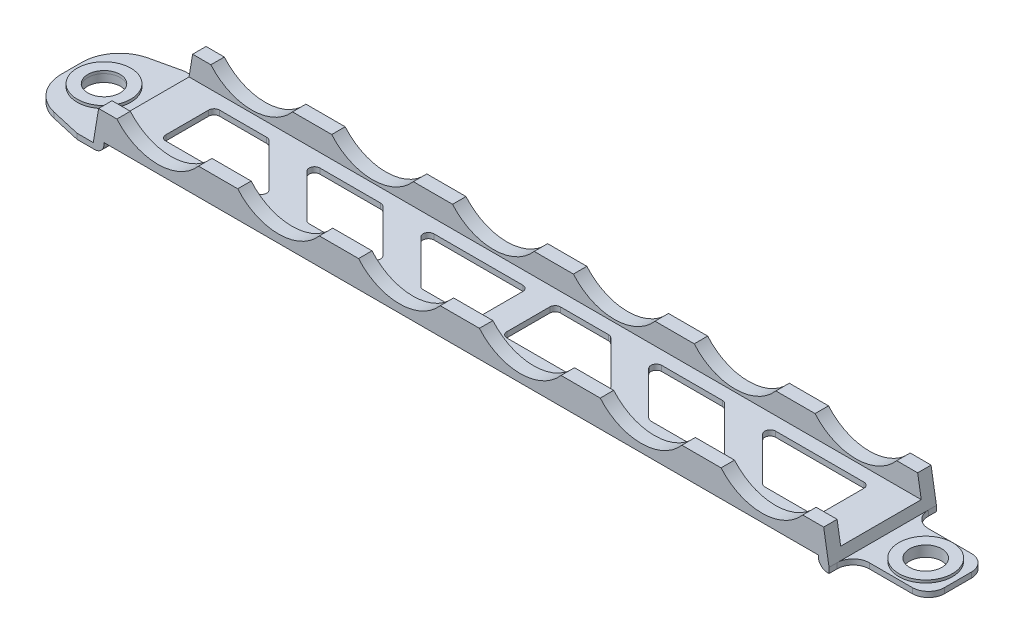
SolidWorks part; units mm, degrees
ref_plane "Front" through (0, 0, 0) normal (0, 0, 1) x (1, 0, 0)
ref_plane "Top" through (0, 0, 0) normal (0, 1, 0) x (1, 0, 0)
ref_plane "Right" through (0, 0, 0) normal (1, 0, 0) x (0, 0, -1)
sketch "Sketch1" plane through (0, 0, 0) normal (0, 1, 0) x (1, 0, 0)
  line L1 (-75.8645, 3.3155) -> (89.1355, 3.3155)
  line L2 (-75.8645, 3.3155) -> (-75.8645, -16.6845)
  line L3 (-75.8645, -16.6845) -> (89.1355, -16.6845)
  line L4 (89.1355, 3.3155) -> (89.1355, -16.6845)
  dimension "D1" = 165
  dimension "D2" = 20
extrude "Extrude1" add sketch "Sketch1" along normal blind 7
sketch "Sketch2" plane through (0, 7, 0) normal (0, 1, 0) x (-1, 0, 0)
  line L0 (-89.1355, 16.6845) -> (-89.1355, -3.3155) construction
  line L1 (75.8645, -0.8155) -> (-89.1355, -0.8155)
  line L2 (75.8645, -0.8155) -> (75.8645, 14.1845)
  line L3 (75.8645, 14.1845) -> (-89.1355, 14.1845)
  line L4 (-89.1355, -0.8155) -> (-89.1355, 14.1845)
  line L5 (75.8645, -3.3155) -> (75.8645, 16.6845) construction
  line L6 (-89.1355, -3.3155) -> (75.8645, -3.3155) construction
  line L7 (75.8645, 16.6845) -> (-89.1355, 16.6845) construction
  dimension "D1" = 2.5
  dimension "D2" = 2.5
extrude "Cut-Extrude2" cut sketch "Sketch2" against normal blind 4
sketch "Sketch3" plane through (0, 0, 16.6845) normal (0, 0, 1) x (1, 0, 0)
  line L0 (-75.8645, 0) -> (89.1355, 0) construction
  line L1 (-83.9413, 1) -> (-61.8645, 1)
  line L2 (-83.9413, 1) -> (-83.9413, 15.5971)
  line L3 (-83.9413, 15.5971) -> (-61.8645, 15.5971)
  line L4 (-61.8645, 1) -> (-61.8645, 15.5971)
  line L5 (-75.8645, 7) -> (-75.8645, 0) construction
  line L6 (6.6355, 7) -> (6.6355, 44.5919) construction
  line L7 (-75.8645, 7) -> (89.1355, 7) construction
  line L8 (75.1355, 1) -> (75.1355, 15.5971)
  line L9 (97.2124, 15.5971) -> (75.1355, 15.5971)
  line L10 (97.2124, 1) -> (97.2124, 15.5971)
  line L11 (97.2124, 1) -> (75.1355, 1)
  line L13 (-59.8645, -11.0368) -> (73.1355, -11.0368)
  line L14 (-59.8645, -11.0368) -> (-59.8645, 2)
  line L15 (-59.8645, 2) -> (73.1355, 2)
  line L16 (73.1355, -11.0368) -> (73.1355, 2)
  dimension "D1" = 1
  dimension "D2" = 14
  dimension "D3" = 2
  dimension "D4" = 2
  dimension "D5" = 2
extrude "Cut-Extrude3" cut sketch "Sketch3" against normal up to next
sketch "Sketch4" plane through (0, 0, 16.6845) normal (0, 0, 1) x (1, 0, 0)
  line L0 (73.1355, 2) -> (-59.8645, 2) construction
  line L1 (-61.8645, 1) -> (-61.8645, 7) construction
  circle A0 centre (-49.8645, 13.5) radius 10
  dimension "D1" = 20
  dimension "D2" = 11.5
  dimension "D3" = 12
extrude "Cut-Extrude4" cut sketch "Sketch4" against normal through all
pattern_linear "LPattern1" count 6 spacing 22.5 along (1, 0, 0) of "Cut-Extrude4"
sketch "Sketch5" plane through (0, 0, 16.6845) normal (0, 0, 1) x (1, 0, 0)
  line L0 (-61.8645, 1) -> (-60.8644, 7)
  line L1 (-60.8644, 7) -> (-64.4402, 7)
  line L2 (-64.4402, 7) -> (-61.8645, 1)
  line L3 (75.1355, 1) -> (74.1355, 7)
  line L4 (74.1355, 7) -> (77.9206, 7)
  line L5 (77.9206, 7) -> (75.1355, 1)
  line L6 (70.2349, 7) -> (75.1355, 7) construction
  line L7 (-61.8645, 7) -> (-57.4638, 7) construction
  dimension "D1" = 1
  dimension "D2" = 1
extrude "Cut-Extrude5" cut sketch "Sketch5" against normal through all
sketch "Sketch6" plane through (0, 1, 0) normal (0, 1, 0) x (-1, 0, 0)
  line L0 (75.8645, 16.6845) -> (61.8645, 16.6845) construction
  line L1 (75.8645, -3.3155) -> (75.8645, 16.6845) construction
  circle A0 centre (69.8645, 6.6845) radius 3
  circle A1 centre (69.8645, 6.6845) radius 5
  dimension "D3" = 10
  dimension "D4" = 6
  dimension "D1" = 10
  dimension "D2" = 6
extrude "Extrude2" add sketch "Sketch6" along normal blind 0.5
sketch "Sketch7" plane through (0, 1, 0) normal (0, 1, 0) x (-1, 0, 0)
  circle A0 centre (69.8645, 6.6845) radius 3.0992
extrude "Cut-Extrude6" cut sketch "Sketch7" against normal up to next
sketch "Sketch8" plane through (0, 1, 0) normal (0, 1, 0) x (-1, 0, 0)
  line L0 (64.8645, -3.3155) -> (75.8645, -11.4554)
  line L1 (61.8645, -3.3155) -> (75.8645, -3.3155) construction
  line L2 (64.8645, -3.3155) -> (70.4158, -2.0539)
  line L3 (75.8645, -3.3155) -> (75.8645, 16.6845) construction
  line L4 (75.8645, 4.7721) -> (75.8645, 8.5969)
  line L5 (70.4158, 15.4228) -> (64.8645, 16.6845)
  line L6 (75.8645, 16.6845) -> (61.8645, 16.6845) construction
  line L7 (75.8645, -11.4554) -> (88.9345, -0.8155)
  line L8 (88.9345, -0.8155) -> (80.3687, 25.9894)
  line L9 (80.3687, 25.9894) -> (64.8645, 16.6845)
  arc A0 (75.8645, 8.5969) -> (70.4158, 15.4228) centre (68.8645, 8.5969) ccw
  arc A1 (75.8645, 4.7721) -> (70.4158, -2.0539) centre (68.8645, 4.7721) cw
  point P21 (75.8645, 14.1845)
  point P24 (75.8645, -0.8155)
  dimension "D5" = 7
  dimension "D6" = 7
  dimension "D1" = 3
  dimension "D2" = 3
  dimension "D3" = 2.5
  dimension "D4" = 2.5
extrude "Cut-Extrude7" cut sketch "Sketch8" against normal up to next
sketch "Sketch9" plane through (0, 0, 0) normal (0, -1, 0) x (1, 0, 0)
  circle A0 centre (-69.8645, 6.6845) radius 5
  circle A1 centre (-69.8645, 6.6845) radius 3.0992
  dimension "D1" = 10
extrude "Extrude3" add sketch "Sketch9" along normal blind 0.5
sketch "Sketch10" plane through (0, 1, 0) normal (0, 1, 0) x (-1, 0, 0)
  line L0 (-89.1355, 16.6845) -> (-89.1355, -3.3155) construction
  line L3 (-89.1355, -3.3155) -> (-75.1355, -3.3155) construction
  circle A0 centre (-83.1355, 6.6845) radius 3
  dimension "D2" = 6
  dimension "D1" = 6
  dimension "D3" = 10
extrude "Cut-Extrude8" cut sketch "Sketch10" against normal up to next
sketch "Sketch11" plane through (0, 1, 0) normal (0, 1, 0) x (-1, 0, 0)
  line L0 (-75.1355, 16.6845) -> (-89.1355, 16.6845) construction
  line L1 (-75.1355, -8.6607) -> (-98.5968, -8.6607)
  line L2 (-98.5968, -8.6607) -> (-98.5968, 22.0296)
  line L3 (-86.1355, 12.1845) -> (-78.1355, 12.1845)
  line L4 (-75.1355, 22.0296) -> (-75.1355, 15.1845)
  line L6 (-89.1355, 6.6845) -> (-106.1726, 6.6845) construction
  line L7 (-89.1355, 16.6845) -> (-89.1355, -3.3155) construction
  line L8 (-75.1355, -8.6607) -> (-75.1355, -1.8155)
  line L9 (-86.1355, 1.1845) -> (-78.1355, 1.1845)
  line L10 (-98.5968, 22.0296) -> (-75.1355, 22.0296)
  line L12 (-89.1355, 4.1845) -> (-89.1355, 9.1845)
  arc A0 (-89.1355, 9.1845) -> (-86.1355, 12.1845) centre (-86.1355, 9.1845) cw
  arc A1 (-89.1355, 4.1845) -> (-86.1355, 1.1845) centre (-86.1355, 4.1845) ccw
  arc A3 (-75.1355, 15.1845) -> (-78.1355, 12.1845) centre (-78.1355, 15.1845) cw
  arc A4 (-75.1355, -1.8155) -> (-78.1355, 1.1845) centre (-78.1355, -1.8155) ccw
  point P14 (-89.1355, 12.1845)
  point P19 (-89.1355, 1.1845)
  point P24 (-75.1355, 12.1845)
  point P25 (-75.1355, 1.1845)
  dimension "D2" = 3
  dimension "D3" = 3
  dimension "D4" = 3
  dimension "D1" = 4.5
extrude "Cut-Extrude9" cut sketch "Sketch11" against normal up to next
sketch "Sketch12" plane through (0, 1, 0) normal (0, 1, 0) x (-1, 0, 0)
  circle A0 centre (-83.1355, 6.6845) radius 3
  circle A1 centre (-83.1355, 6.6845) radius 5
  dimension "D1" = 10
extrude "Extrude4" add sketch "Sketch12" along normal blind 0.5
sketch "Sketch13" plane through (0, 0, 0) normal (0, -1, 0) x (1, 0, 0)
  circle A0 centre (83.1355, 6.6845) radius 3
  circle A1 centre (83.1355, 6.6845) radius 5
  dimension "D1" = 10
extrude "Extrude5" add sketch "Sketch13" along normal blind 0.5
sketch "Sketch14" plane through (0, 3, 0) normal (0, 1, 0) x (-1, 0, 0)
  line L0 (-75.1355, -1.8155) -> (-75.1355, 15.1845) construction
  line L1 (53.3645, 1.6845) -> (44.5629, 1.6845)
  line L2 (54.3645, 2.6845) -> (54.3645, 10.6845)
  line L3 (53.3645, 11.6845) -> (36.5629, 11.6845)
  line L4 (-67.6355, 2.6845) -> (-67.6355, 10.6845)
  line L5 (61.8645, -3.3155) -> (61.8645, 16.6845) construction
  line L6 (34.9638, -3.3155) -> (42.2651, -3.3155) construction
  line L7 (-4.1355, 2.6845) -> (-4.1355, 10.6845)
  line L8 (-9.1355, 2.6845) -> (-9.1355, 10.6845)
  line L9 (-10.1355, 1.6845) -> (-19.0767, 1.6845)
  line L10 (-10.1355, 11.6845) -> (-27.0767, 11.6845)
  line L11 (14.1574, 3.3916) -> (6.1574, 11.3916)
  line L12 (37.0777, 1.6845) -> (27.0777, 11.6845) construction
  line L13 (22.9355, 1.6845) -> (12.9355, 11.6845) construction
  line L14 (15.8645, 1.6845) -> (5.8645, 11.6845) construction
  line L15 (-19.4909, 1.6845) -> (-29.4909, 11.6845) construction
  line L16 (22.6426, 1.9774) -> (14.6426, 9.9774)
  line L17 (19.4, 5.22) -> (9.4, 15.22) construction
  line L18 (13.4503, 1.6845) -> (-3.1355, 1.6845)
  line L19 (5.4503, 11.6845) -> (-3.1355, 11.6845)
  line L20 (-26.5619, 1.6845) -> (-36.5619, 11.6845) construction
  line L21 (-40.7041, 1.6845) -> (-50.7041, 11.6845) construction
  line L24 (35.3706, 3.3916) -> (27.3706, 11.3916)
  line L25 (30.0066, 8.7555) -> (20.0066, 18.7555) construction
  line L26 (43.8558, 1.9774) -> (35.8558, 9.9774)
  line L27 (40.6132, 5.22) -> (30.6132, 15.22) construction
  line L28 (34.6635, 1.6845) -> (23.3497, 1.6845)
  line L29 (26.6635, 11.6845) -> (15.3497, 11.6845)
  line L30 (-19.7838, 1.9774) -> (-27.7838, 9.9774)
  line L31 (-1.8132, -15.9932) -> (-11.8132, -5.9932) construction
  line L32 (-28.269, 3.3916) -> (-36.269, 11.3916)
  line L33 (-23.0264, -1.8511) -> (-33.0264, 8.1489) construction
  line L34 (-28.9762, 1.6845) -> (-40.2899, 1.6845)
  line L35 (-36.9762, 11.6845) -> (-48.2899, 11.6845)
  line L36 (-40.997, 1.9774) -> (-48.997, 9.9774)
  line L37 (-33.633, -5.3866) -> (-43.633, 4.6134) construction
  line L38 (-49.4823, 3.3916) -> (-57.4823, 11.3916)
  line L39 (-44.2396, -1.8511) -> (-54.2396, 8.1489) construction
  line L40 (-50.1894, 1.6845) -> (-66.6355, 1.6845)
  line L41 (-58.1894, 11.6845) -> (-66.6355, 11.6845)
  arc A0 (36.5629, 11.6845) -> (35.8558, 9.9774) centre (36.5629, 10.6845) ccw
  arc A1 (34.6635, 1.6845) -> (35.3706, 3.3916) centre (34.6635, 2.6845) ccw
  arc A2 (15.3497, 11.6845) -> (14.6426, 9.9774) centre (15.3497, 10.6845) ccw
  arc A3 (14.1574, 3.3916) -> (13.4503, 1.6845) centre (13.4503, 2.6845) cw
  arc A4 (27.3706, 11.3916) -> (26.6635, 11.6845) centre (26.6635, 10.6845) ccw
  arc A5 (23.3497, 1.6845) -> (22.6426, 1.9774) centre (23.3497, 2.6845) cw
  arc A6 (44.5629, 1.6845) -> (43.8558, 1.9774) centre (44.5629, 2.6845) cw
  arc A7 (54.3645, 2.6845) -> (53.3645, 1.6845) centre (53.3645, 2.6845) cw
  arc A8 (53.3645, 11.6845) -> (54.3645, 10.6845) centre (53.3645, 10.6845) cw
  arc A9 (5.4503, 11.6845) -> (6.1574, 11.3916) centre (5.4503, 10.6845) cw
  arc A10 (-3.1355, 11.6845) -> (-4.1355, 10.6845) centre (-3.1355, 10.6845) ccw
  arc A11 (-3.1355, 1.6845) -> (-4.1355, 2.6845) centre (-3.1355, 2.6845) cw
  arc A12 (-19.0767, 1.6845) -> (-19.7838, 1.9774) centre (-19.0767, 2.6845) cw
  arc A13 (-9.1355, 2.6845) -> (-10.1355, 1.6845) centre (-10.1355, 2.6845) cw
  arc A14 (-10.1355, 11.6845) -> (-9.1355, 10.6845) centre (-10.1355, 10.6845) cw
  arc A15 (-27.7838, 9.9774) -> (-27.0767, 11.6845) centre (-27.0767, 10.6845) cw
  arc A16 (-28.9762, 1.6845) -> (-28.269, 3.3916) centre (-28.9762, 2.6845) ccw
  arc A17 (-36.269, 11.3916) -> (-36.9762, 11.6845) centre (-36.9762, 10.6845) ccw
  arc A18 (-40.997, 1.9774) -> (-40.2899, 1.6845) centre (-40.2899, 2.6845) ccw
  arc A19 (-48.2899, 11.6845) -> (-48.997, 9.9774) centre (-48.2899, 10.6845) ccw
  arc A20 (-50.1894, 1.6845) -> (-49.4823, 3.3916) centre (-50.1894, 2.6845) ccw
  arc A21 (-58.1894, 11.6845) -> (-57.4823, 11.3916) centre (-58.1894, 10.6845) cw
  arc A22 (-67.6355, 10.6845) -> (-66.6355, 11.6845) centre (-66.6355, 10.6845) cw
  arc A23 (-66.6355, 1.6845) -> (-67.6355, 2.6845) centre (-66.6355, 2.6845) cw
  point P18 (0, 0)
  point P50 (37.0777, 1.6845)
  point P57 (15.8645, 1.6845)
  point P77 (-4.1355, 1.6845)
  point P83 (-9.1355, 1.6845)
  point P86 (-9.1355, 11.6845)
  point P93 (-26.5619, 1.6845)
  point P105 (-47.7751, 1.6845)
  point P108 (-57.7751, 11.6845)
  dimension "D16" = 1
  dimension "D1" = 7.5
  dimension "D2" = 7.5
  dimension "D3" = 5
  dimension "D4" = 10
  dimension "D5" = 58.5
  dimension "D6" = 5
  dimension "D7" = 20
  dimension "D9" = 5
  dimension "D10" = 10
  dimension "D11" = 5
  dimension "D12" = 25
  dimension "D13" = 5
  dimension "D14" = 10
  dimension "D15" = 5
extrude "Cut-Extrude10" cut sketch "Sketch14" against normal up to next
fillet "Fillet1" radius 1.75 2 edges at (-59.8645, 0, 6.6845) (73.1355, 0, 6.6845)
